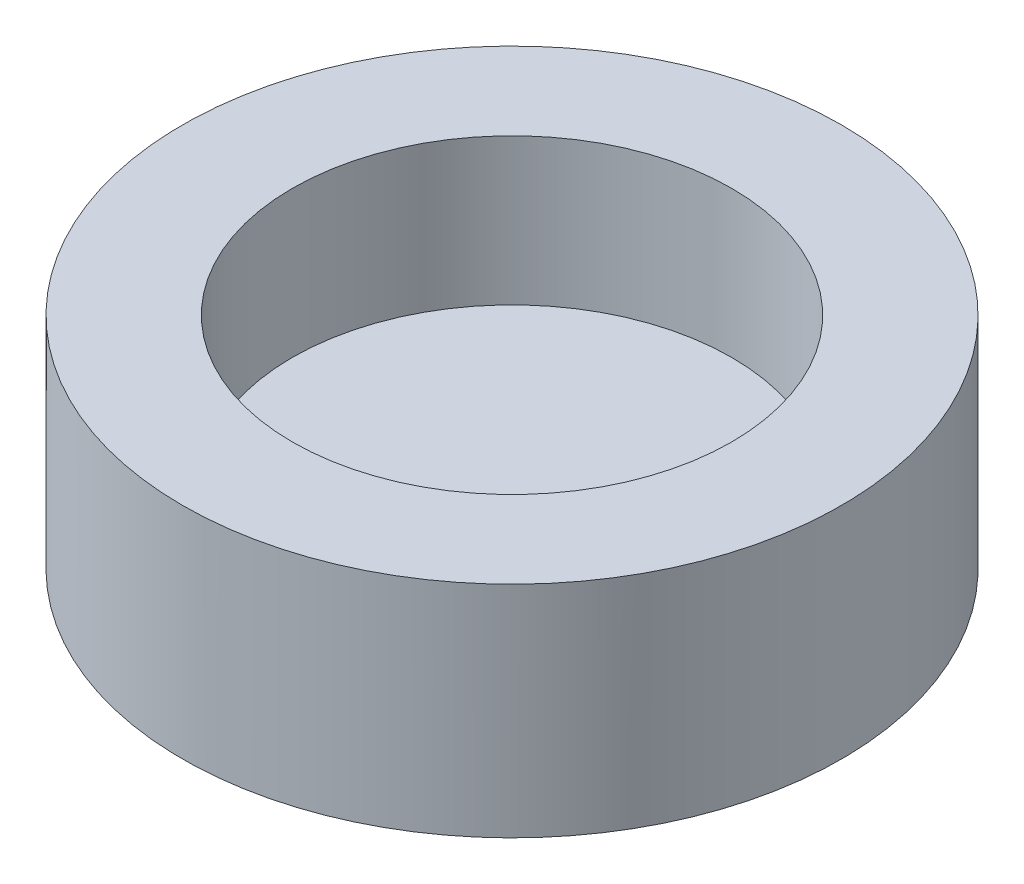
SolidWorks part; units mm, degrees
ref_plane "Front Plane" through (0, 0, 0) normal (0, 0, 1) x (1, 0, 0)
ref_plane "Top Plane" through (0, 0, 0) normal (0, 1, 0) x (1, 0, 0)
ref_plane "Right Plane" through (0, 0, 0) normal (1, 0, 0) x (0, 0, -1)
sketch "Sketch1" plane through (0, 0, 0) normal (0, 1, 0) x (1, 0, 0)
  circle A0 centre (0, 0) radius 15
  circle A1 centre (0, 0) radius 22.5
  dimension "D1" = 30
  dimension "D2" = 45
extrude "Boss-Extrude1" add sketch "Sketch1" along normal blind 10
sketch "Sketch2" plane through (0, 0, 0) normal (0, -1, 0) x (1, 0, 0)
  circle A0 centre (0, 0) radius 22.5
extrude "Boss-Extrude2" add sketch "Sketch2" along normal blind 5
